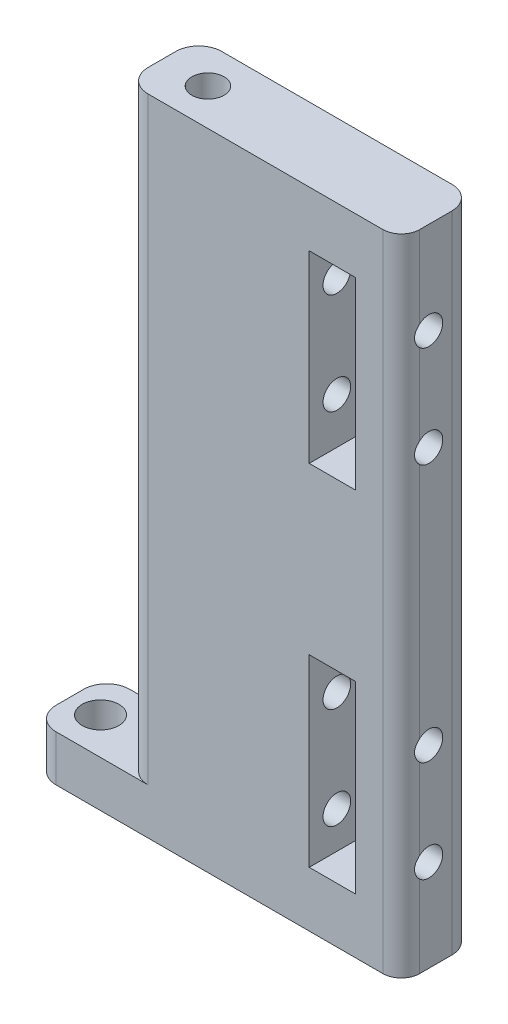
SolidWorks part; units mm, degrees
material "ABS"
ref_plane "Plano frontal" through (0, 0, 0) normal (0, 0, 1) x (1, 0, 0)
ref_plane "Plano superior" through (0, 0, 0) normal (0, 1, 0) x (1, 0, 0)
ref_plane "Plano direito" through (0, 0, 0) normal (1, 0, 0) x (0, 0, -1)
sketch "Esboço2" plane through (0, 0, 0) normal (0, 0, 1) x (1, 0, 0)
  line L1 (-67.2812, 34.8924) -> (-37.2812, 34.8924)
  line L2 (-67.2812, 34.8924) -> (-67.2812, -35.1076)
  line L3 (-67.2812, -35.1076) -> (-37.2812, -35.1076)
  line L4 (-37.2812, 34.8924) -> (-37.2812, -35.1076)
extrude "Ressalto-extrusão1" add sketch "Esboço2" along normal blind 8
sketch "Esboço3" plane through (0, -35.1076, 0) normal (0, -1, 0) x (-1, 0, 0)
  line L0 (50.5731, -0.27) -> (50.5731, -7.73) construction
  line L1 (50.5731, -7.73) -> (50.1981, -7.73) construction
  line L3 (55.6594, -4) -> (67.2812, -4) construction
  line L4 (67.2812, -8) -> (67.2812, 0) construction
  line L5 (67.2812, 0) -> (37.2812, 0) construction
  line L7 (50.5731, -7.73) -> (50.9481, -7.73) construction
  circle A5 centre (58.2812, -4) radius 0.75
  circle A7 centre (63.2812, -4) radius 0.75
  dimension "D1" = 4
  dimension "D2" = 5
  dimension "D7" = 7.46
  dimension "D8" = 0.27
  dimension "D9" = 0
extrude "Corte-extrusão1" cut sketch "Esboço3" against normal blind 30
fillet "Filete1" radius 2 1 edges at (-37.2812, -0.1076, 8)
sketch "Esboço17" plane through (0, 0, 0) normal (0, 0, -1) x (-1, 0, 0)
  line L1 (67.2812, -35.1076) -> (77.2812, -35.1076)
  line L2 (67.2812, -35.1076) -> (67.2812, -30.1076)
  line L3 (67.2812, -30.1076) -> (77.2812, -30.1076)
  line L4 (77.2812, -35.1076) -> (77.2812, -30.1076)
extrude "Ressalto-extrusão4" add sketch "Esboço17" against normal blind 8
sketch "Esboço20" plane through (0, -35.1076, 0) normal (0, -1, 0) x (1, 0, 0)
  line L0 (-77.2812, 8) -> (-39.2812, 8) construction
  circle A0 centre (-73.9512, 4) radius 2
  circle A1 centre (-63.2812, 4) radius 0.75 construction
  dimension "D1" = 4
  dimension "D2" = 10.67
extrude "Corte-extrusão9" cut sketch "Esboço20" against normal blind 8 contours A0
fillet "Filete2" radius 2.5 1 edges at (-67.2812, 2.3924, 8)
fillet "Filete3" radius 2.5 1 edges at (-67.2812, 2.3924, 0)
fillet "Filete4" radius 2.5 1 edges at (-77.2812, -32.6076, 8)
fillet "Filete5" radius 2.5 1 edges at (-77.2812, -32.6076, 0)
sketch "Esboço21" plane through (0, 0, 8) normal (0, 0, 1) x (1, 0, 0)
  line L0 (-39.2812, 34.8924) -> (-64.7812, 34.8924) construction
  line L1 (-47.2812, 28.8924) -> (-42.2812, 28.8924)
  line L2 (-47.2812, 28.8924) -> (-47.2812, 8.8924)
  line L3 (-47.2812, 8.8924) -> (-42.2812, 8.8924)
  line L4 (-42.2812, 28.8924) -> (-42.2812, 8.8924)
  line L5 (-39.2812, -35.1076) -> (-39.2812, 34.8924) construction
  line L6 (-74.7812, -35.1076) -> (-39.2812, -35.1076) construction
  line L7 (-42.2812, -29.1076) -> (-47.2812, -29.1076)
  line L8 (-42.2812, -29.1076) -> (-42.2812, -9.1076)
  line L9 (-42.2812, -9.1076) -> (-47.2812, -9.1076)
  line L10 (-47.2812, -29.1076) -> (-47.2812, -9.1076)
  dimension "D1" = 6
  dimension "D2" = 20
  dimension "D3" = 3
  dimension "D4" = 5
  dimension "D5" = 6
  dimension "D6" = 20
  dimension "D7" = 5
  dimension "D8" = 3
extrude "Corte-extrusão10" cut sketch "Esboço21" against normal through all
fillet "Filete6" radius 2.5 1 edges at (-37.2812, -0.1076, 0)
sketch "Esboço22" plane through (-37.2812, 0, 0) normal (1, 0, 0) x (0, 0, -1)
  line L0 (-6, -35.1076) -> (-2.5, -35.1076) construction
  line L1 (-6, 34.8924) -> (-2.5, 34.8924) construction
  line L2 (-8, -35.1076) -> (-8, 34.8924) construction
  circle A0 centre (-5, -25.1076) radius 1.5
  circle A1 centre (-5, -14.1076) radius 1.5
  circle A2 centre (-5, 24.8924) radius 1.5
  circle A3 centre (-5, 13.8924) radius 1.5
  dimension "D1" = 3
  dimension "D2" = 3
  dimension "D3" = 10
  dimension "D4" = 11
  dimension "D5" = 3
  dimension "D6" = 3
  dimension "D7" = 10
  dimension "D8" = 11
  dimension "D9" = 3
  dimension "D10" = 3
extrude "Corte-extrusão11" cut sketch "Esboço22" against normal blind 20
sketch "Esboço23" plane through (0, 34.8924, 0) normal (0, 1, 0) x (1, 0, 0)
  line L0 (-67.2812, -5.5) -> (-67.2812, -2.5) construction
  line L1 (-39.7812, 0) -> (-64.7812, 0) construction
  circle A0 centre (-62.2812, -4) radius 1.75
  dimension "D1" = 3.5
  dimension "D2" = 5
  dimension "D3" = 4
extrude "Corte-extrusão12" cut sketch "Esboço23" against normal blind 22
